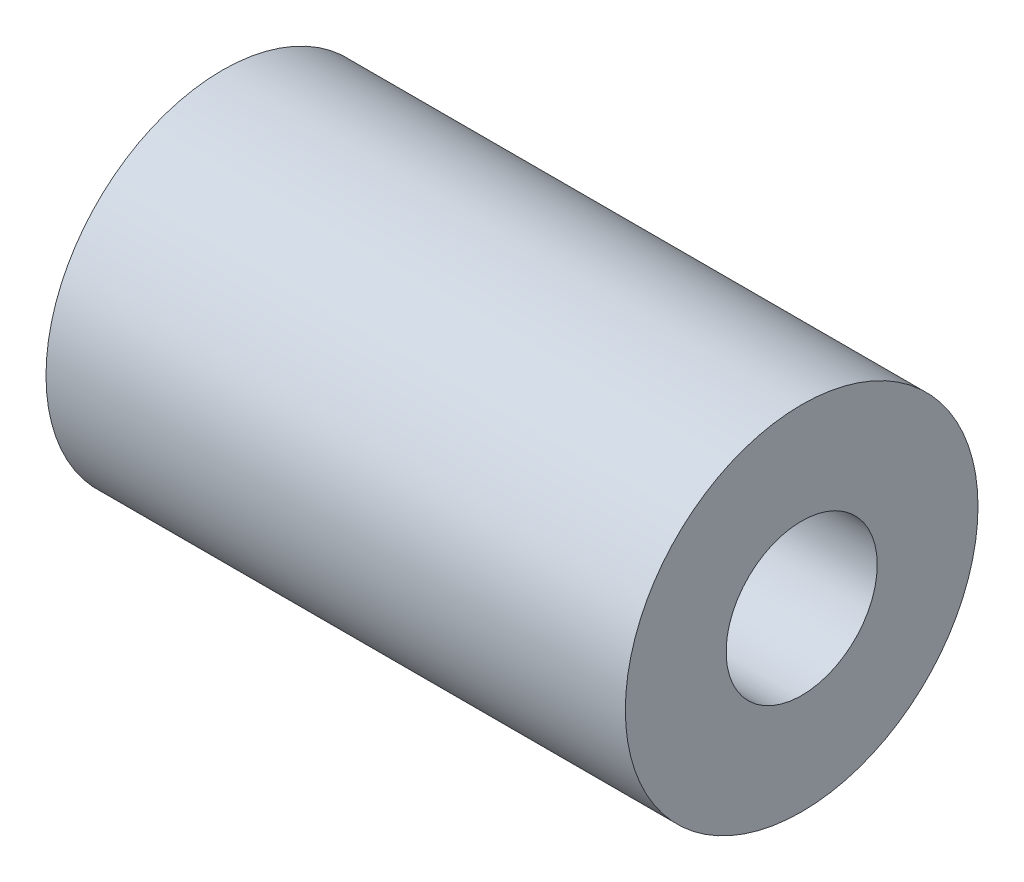
SolidWorks part; units mm, degrees
ref_plane "前视基准面" through (0, 0, 0) normal (0, 0, 1) x (1, 0, 0)
ref_plane "上视基准面" through (0, 0, 0) normal (0, 1, 0) x (1, 0, 0)
ref_plane "右视基准面" through (0, 0, 0) normal (1, 0, 0) x (0, 0, -1)
sketch "草图1" plane through (0, 0, 0) normal (1, 0, 0) x (0, 0, -1)
  circle A0 centre (0, 0) radius 1.5
  circle A1 centre (0, 0) radius 3.5
  dimension "D1" = 3
  dimension "D2" = 7
extrude "凸台-拉伸1" add sketch "草图1" along normal blind 11.5
